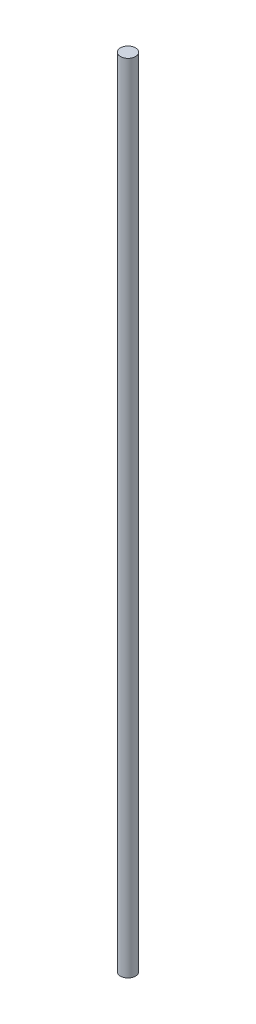
SolidWorks part; units mm, degrees
ref_plane "Front Plane" through (0, 0, 0) normal (0, 0, 1) x (1, 0, 0)
ref_plane "Top Plane" through (0, 0, 0) normal (0, 1, 0) x (1, 0, 0)
ref_plane "Right Plane" through (0, 0, 0) normal (1, 0, 0) x (0, 0, -1)
sketch "Sketch1" plane through (0, 0, 0) normal (0, 1, 0) x (1, 0, 0)
  circle A0 centre (0, 0) radius 0.95
  dimension "D1" = 1.9
extrude "Boss-Extrude1" add sketch "Sketch1" along normal blind 100
